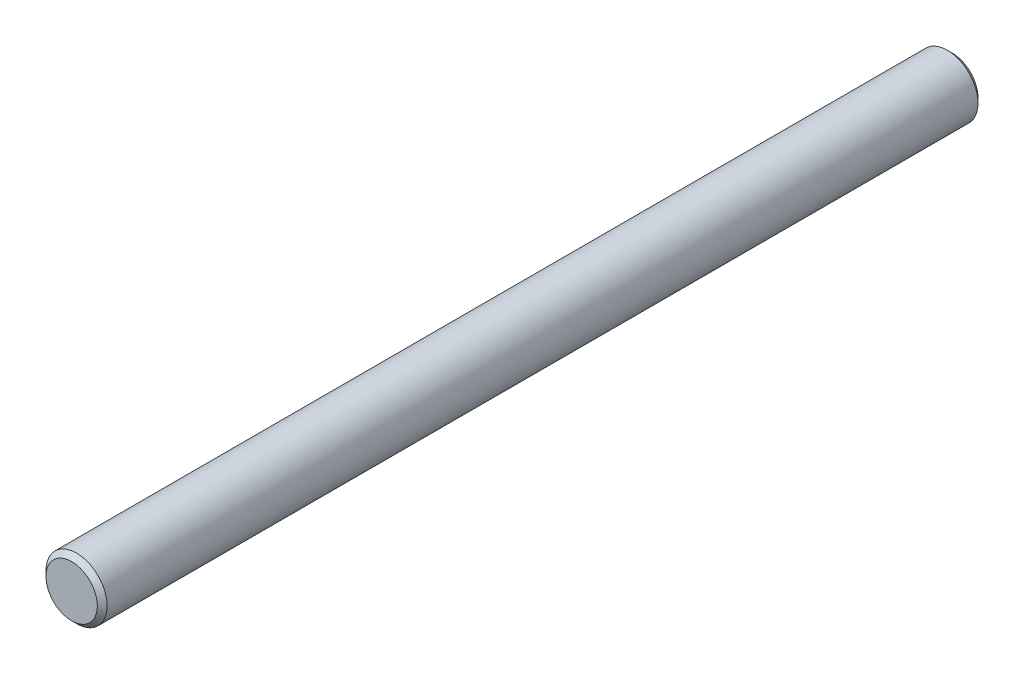
SolidWorks part; units mm, degrees
material "6061-T6 (SS)"
ref_plane "Front Plane" through (0, 0, 0) normal (0, 0, 1) x (1, 0, 0)
ref_plane "Top Plane" through (0, 0, 0) normal (0, 1, 0) x (1, 0, 0)
ref_plane "Right Plane" through (0, 0, 0) normal (1, 0, 0) x (0, 0, -1)
sketch "Sketch1" plane through (0, 0, 0) normal (0, 0, 1) x (1, 0, 0)
  circle A0 centre (0, 0) radius 1.5875
  dimension "D1" = 3.175
extrude "Boss-Extrude1" add sketch "Sketch1" along normal blind 45.72
chamfer "Chamfer1" distance 0.254 angle 45 2 edges at (1.5875, 0, 45.72) (1.5875, 0, 0)
